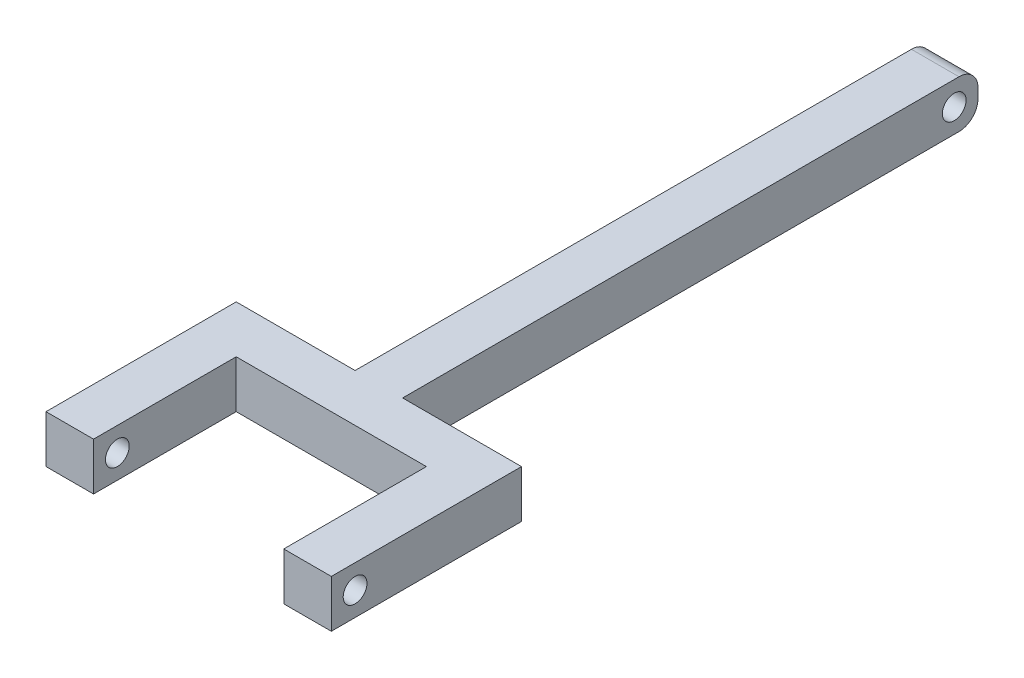
SolidWorks part; units mm, degrees
ref_plane "Front Plane" through (0, 0, 0) normal (0, 0, 1) x (1, 0, 0)
ref_plane "Top Plane" through (0, 0, 0) normal (0, 1, 0) x (1, 0, 0)
ref_plane "Right Plane" through (0, 0, 0) normal (1, 0, 0) x (0, 0, -1)
sketch "Sketch1" plane through (0, 0, 0) normal (0, 0, 1) x (1, 0, 0)
  line L1 (-6.35, -6.35) -> (6.35, -6.35)
  line L2 (-6.35, -6.35) -> (-6.35, 6.35)
  line L3 (-6.35, 6.35) -> (6.35, 6.35)
  line L4 (6.35, -6.35) -> (6.35, 6.35)
  point P4 (0, 6.35)
  point P6 (-6.35, 0)
  dimension "D1" = 12.7
  dimension "D2" = 12.7
  dimension "D3" = 0
  dimension "D4" = 0
extrude "Boss-Extrude1" add sketch "Sketch1" against normal blind 80.01 and the other way blind 86.36
sketch "Sketch4" plane through (0, 0, 0) normal (1, 0, 0) x (0, 0, -1)
  line L0 (-86.36, 6.35) -> (-86.36, -6.35)
  line L1 (-86.36, -6.35) -> (-73.66, -6.35)
  line L2 (-73.66, -6.35) -> (-73.66, 6.35)
  line L3 (-73.66, 6.35) -> (-86.36, 6.35)
  dimension "D1" = 12.7
extrude "Boss-Extrude2" add sketch "Sketch4" along normal mid plane 76.2
sketch "Sketch5" plane through (0, 0, 73.66) normal (0, 0, -1) x (-1, 0, 0)
  line L0 (-38.1, 6.35) -> (-6.35, 6.35) construction
  line L1 (-38.1, -6.35) -> (-25.4, -6.35)
  line L2 (-38.1, -6.35) -> (-38.1, 6.35)
  line L3 (-38.1, 6.35) -> (-25.4, 6.35)
  line L4 (-25.4, -6.35) -> (-25.4, 6.35)
  dimension "D1" = 12.7
extrude "Boss-Extrude3" add sketch "Sketch5" against normal blind 50.8
sketch "Sketch6" plane through (25.4, 0, 0) normal (-1, 0, 0) x (0, 0, 1)
  line L1 (124.46, -6.35) -> (124.46, 6.35) construction
  circle A0 centre (118.11, 0) radius 3.175
  dimension "D1" = 6.35
  dimension "D2" = 6.35
extrude "Cut-Extrude1" cut sketch "Sketch6" against normal blind 16.51
mirror "Mirror1" about plane through (0, 0, 0) normal (1, 0, 0) of "Cut-Extrude1", "Boss-Extrude3"
sketch "Sketch7" plane through (-6.35, 0, 0) normal (-1, 0, 0) x (0, 0, 1)
  line L1 (-80.01, 6.35) -> (-80.01, -6.35) construction
  line L2 (73.66, 6.35) -> (-80.01, 6.35) construction
  circle A0 centre (-73.66, 0) radius 3.175
  point P2 (-80.01, 0)
  dimension "D1" = 6.35
  dimension "D2" = 6.35
extrude "Cut-Extrude2" cut sketch "Sketch7" against normal through all
fillet "Fillet1" radius 5.08 2 edges at (0, -6.35, -80.01) (0, 6.35, -80.01)
